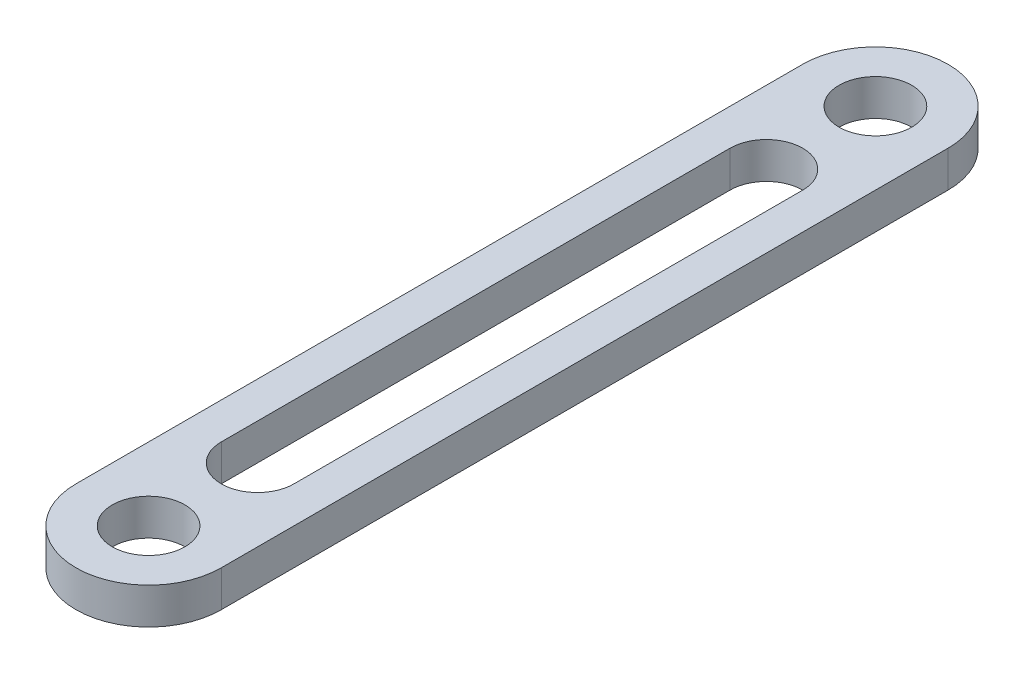
SolidWorks part; units mm, degrees
ref_plane "Front Plane" through (0, 0, 0) normal (0, 0, 1) x (1, 0, 0)
ref_plane "Top Plane" through (0, 0, 0) normal (0, 1, 0) x (1, 0, 0)
ref_plane "Right Plane" through (0, 0, 0) normal (1, 0, 0) x (0, 0, -1)
sketch "Sketch1" plane through (0, 0, 0) normal (0, 1, 0) x (1, 0, 0)
  line L0 (0, 0) -> (0, 100) construction
  line L1 (-10, 0) -> (-10, 100)
  line L2 (10, 0) -> (10, 100)
  line L3 (0, 85) -> (0, 15) construction
  line L4 (5, 85) -> (5, 15)
  line L5 (-5, 85) -> (-5, 15)
  arc A0 (-10, 0) -> (10, 0) centre (0, 0) ccw
  arc A1 (10, 100) -> (-10, 100) centre (0, 100) ccw
  circle A2 centre (0, 0) radius 5
  circle A3 centre (0, 100) radius 5
  arc A4 (5, 85) -> (-5, 85) centre (0, 85) ccw
  arc A5 (-5, 15) -> (5, 15) centre (0, 15) ccw
  point P3 (0, 50)
  point P14 (0, 50)
  dimension "D2" = 10
  dimension "D3" = 10
  dimension "D5" = 70
  dimension "D6" = 5
  dimension "D7" = 100
  dimension "D1" = 100
  dimension "D4" = 2
extrude "Boss-Extrude1" add sketch "Sketch1" along normal blind 5
